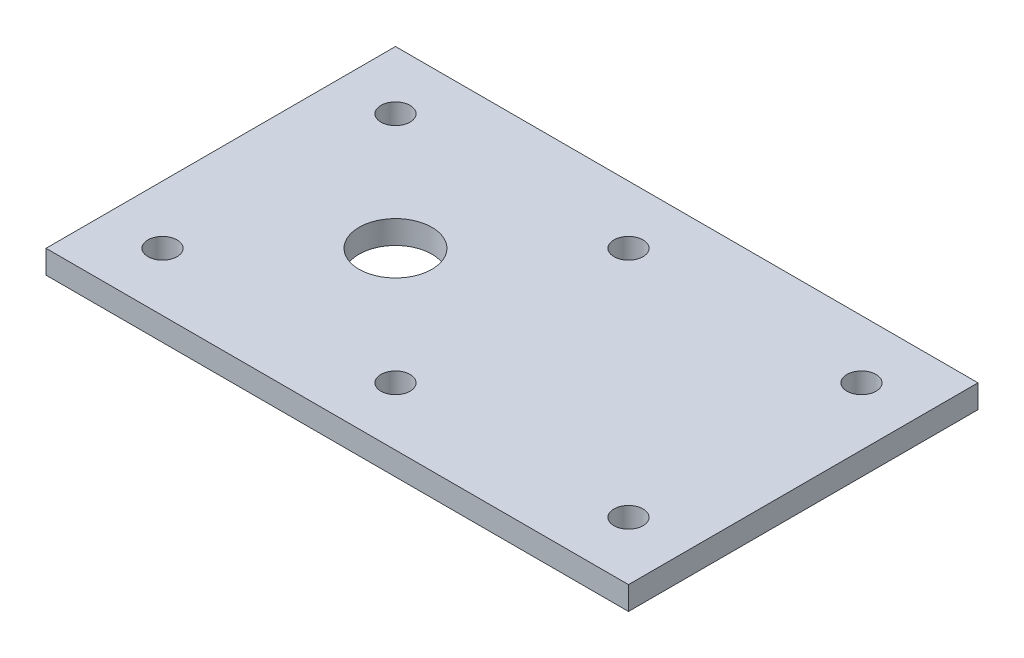
SolidWorks part; units mm, degrees
ref_plane "Front Plane" through (0, 0, 0) normal (0, 0, 1) x (1, 0, 0)
ref_plane "Top Plane" through (0, 0, 0) normal (0, 1, 0) x (1, 0, 0)
ref_plane "Right Plane" through (0, 0, 0) normal (1, 0, 0) x (0, 0, -1)
sketch "Sketch1" plane through (0, 0, 0) normal (0, 1, 0) x (1, 0, 0)
  line L0 (-60, 0) -> (140, 0) construction
  line L9 (140, 60) -> (-60, 60)
  line L10 (140, 60) -> (140, -60)
  line L11 (140, -60) -> (-60, -60)
  line L12 (-60, 60) -> (-60, -60)
  dimension "D1" = 60
  dimension "D2" = 200
  dimension "D3" = 120
extrude "Boss-Extrude3" add sketch "Sketch1" along normal blind 8
sketch "Sketch2" plane through (0, 8, 0) normal (0, 1, 0) x (1, 0, 0)
  circle A0 centre (-40, 40) radius 5
  dimension "D3" = 10
  dimension "D1" = 20
  dimension "D2" = 20
extrude "Cut-Extrude1" cut sketch "Sketch2" against normal through all contours A0
pattern_linear "LPattern5" count 2 spacing 80 along (0, 0, 1) count 3 spacing 80 along (1, 0, 0) of "Cut-Extrude1"
sketch "Sketch3" plane through (0, 8, 0) normal (0, 1, 0) x (1, 0, 0)
  circle A0 centre (0, 0) radius 12.5
  dimension "D1" = 25
extrude "Cut-Extrude2" cut sketch "Sketch3" against normal blind 10
